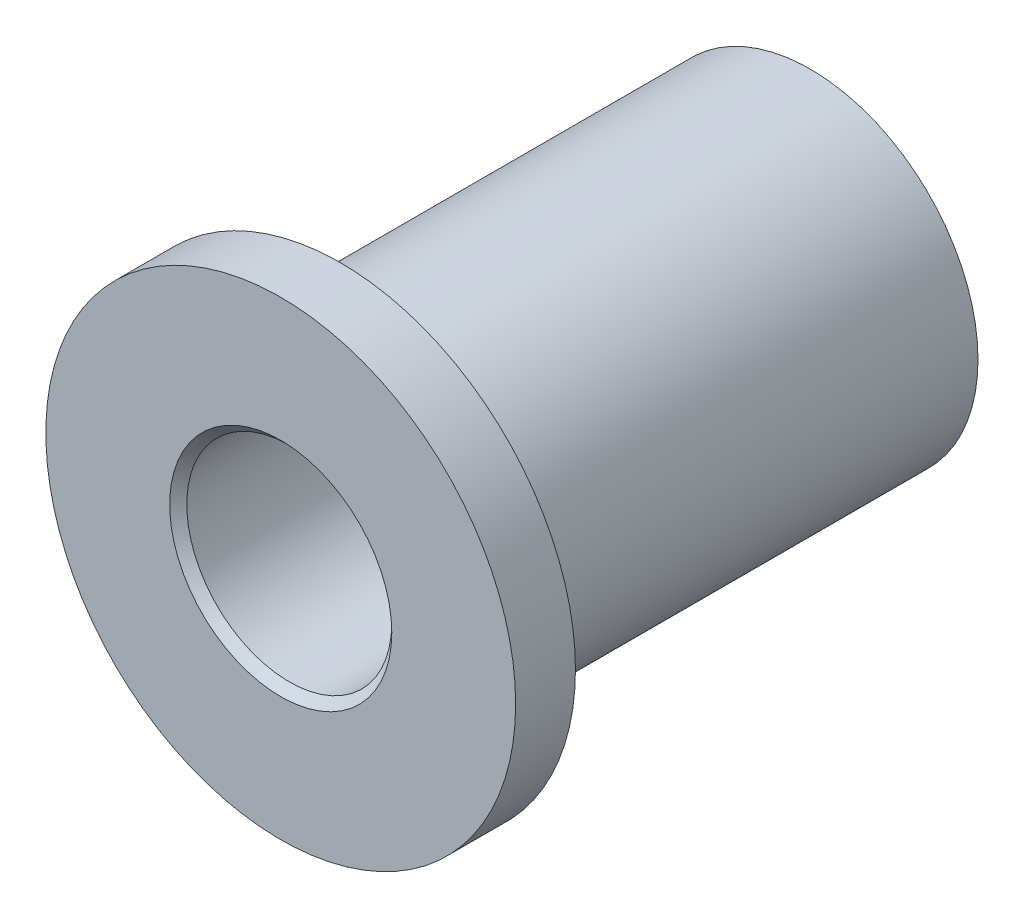
SolidWorks part; units mm, degrees
material "Aluminum Bronze"
ref_plane "Front Plane" through (0, 0, 0) normal (0, 0, 1) x (1, 0, 0)
ref_plane "Top Plane" through (0, 0, 0) normal (0, 1, 0) x (1, 0, 0)
ref_plane "Right Plane" through (0, 0, 0) normal (1, 0, 0) x (0, 0, -1)
sketch "Sketch1" plane through (0, 0, 0) normal (0, 0, 1) x (1, 0, 0)
  circle A0 centre (0, 0) radius 5.5
  dimension "D1" = 11
extrude "Extrude1" add sketch "Sketch1" against normal blind 1.4
sketch "Sketch2" plane through (0, 0, -1.4) normal (0, 0, -1) x (-1, 0, 0)
  circle A0 centre (0, 0) radius 3.925
  dimension "D1" = 7.85
extrude "Extrude2" add sketch "Sketch2" along normal blind 11
sketch "Sketch4" plane through (0, 0, 0) normal (0, 0, 1) x (1, 0, 0)
  circle A0 centre (0, 0) radius 2.4
  dimension "D1" = 4.8
extrude "Cut-Extrude1" cut sketch "Sketch4" against normal through all
chamfer "Chamfer1" distance 0.2 angle 45 1 edges at (2.4, 0, 0)
